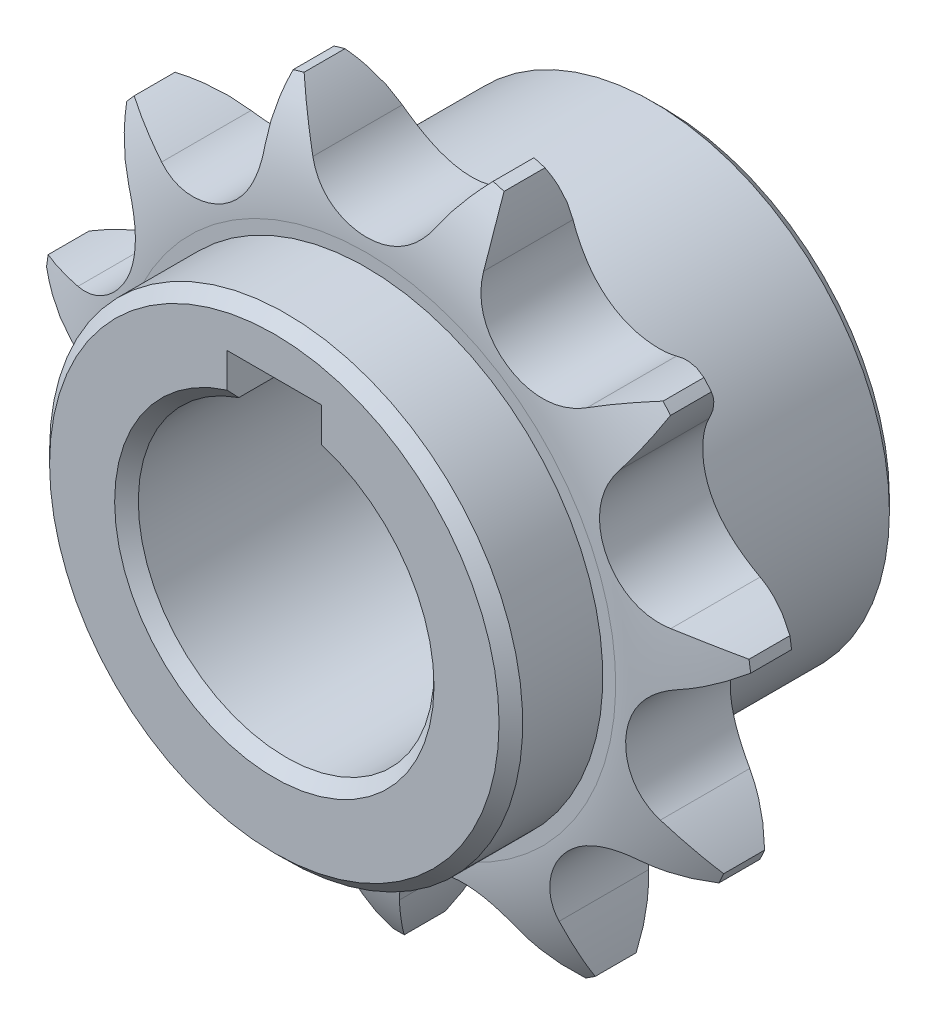
SolidWorks part; units mm, degrees
material "AISI 1045 钢，冷拔"
ref_plane "前视基准面" through (0, 0, 0) normal (0, 0, 1) x (1, 0, 0)
ref_plane "上视基准面" through (0, 0, 0) normal (0, 1, 0) x (1, 0, 0)
ref_plane "右视基准面" through (0, 0, 0) normal (1, 0, 0) x (0, 0, -1)
sketch "草图1" plane through (0, 0, 0) normal (0, 0, 1) x (1, 0, 0)
  line L0 (-28.1739, 0) -> (28.1739, 0) construction
  line L1 (0, 28.1739) -> (0, -28.1739) construction
  line L2 (0, 0) -> (15.232, 23.7014) construction
  line L3 (0, 28.1739) -> (24.3993, 14.087) construction
  line L4 (15.232, 23.7014) -> (-12.91, 25.042) construction
  line L5 (0, 22.1739) -> (0, 0)
  line L6 (0, 0) -> (11.9881, 18.6539)
  circle A0 centre (0, 0) radius 28.1739 construction
  arc A1 (0, 22.1739) -> (5.1962, 25.1739) centre (0, 28.1739) ccw
  arc A2 (9.2388, 23.9869) -> (11.9881, 18.6539) centre (15.232, 23.7014) ccw
  arc A3 (7.9868, 28.9173) -> (5.1962, 25.1739) centre (22.5167, 15.1739) ccw
  arc A4 (9.2388, 23.9869) -> (8.915, 28.6448) centre (-10.7386, 24.9385) ccw
  arc A5 (8.915, 28.6448) -> (7.9868, 28.9173) centre (0, 0) ccw
  dimension "D1" = 56.3478
  dimension "D3" = 12
  dimension "D4" = 12
  dimension "D7" = 40
  dimension "D8" = 40
  dimension "D9" = 60
  dimension "D2" = 32.727
  dimension "D5" = 60
  dimension "D6" = 60
extrude "凸台-拉伸1" add sketch "草图1" along normal blind 8.93
pattern_circular "阵列(圆周)1" count 11 over 360 about axis through (0, 0, 0) along (0, 0, 1) of "凸台-拉伸1"
sketch "草图2" plane through (0, 0, 0) normal (1, 0, 0) x (0, 0, -1)
  line L0 (-4.465, 28.9173) -> (-4.465, -29.9961) construction
  line L1 (-8.93, 28.9173) -> (0, 28.9173) construction
  line L2 (-8.93, -29.9961) -> (0, -29.9961) construction
  line L3 (-8.93, 28.9173) -> (-8.93, -29.9961) construction
  line L4 (0, 28.9173) -> (0, -29.9961) construction
  line L5 (-6.8663, 28.9173) -> (-6.8663, -29.9961) construction
  line L6 (0, 0) -> (-8.93, 0) construction
  line L10 (-2.0638, 28.9173) -> (-2.0638, -29.9961) construction
  line L11 (-8.93, 21.0901) -> (-8.93, 33.5648)
  line L12 (-8.93, 33.5648) -> (0, 33.5648)
  line L13 (0, 33.5648) -> (0, 21.0901)
  arc A1 (-4.465, 32.1277) -> (-8.93, 21.0901) centre (6.945, 21.0901) ccw
  arc A2 (0, 21.0901) -> (-4.465, 32.1277) centre (-15.875, 21.0901) ccw
  dimension "D3" = 31.75
  dimension "D4" = 31.75
  dimension "D1" = 2.0638
  dimension "D2" = 2.0638
revolve "切除-旋转1" cut sketch "草图2" angle 360 about L6
sketch "草图3" plane through (0, 0, 8.93) normal (0, 0, 1) x (1, 0, 0)
  circle A0 centre (0, 0) radius 20
  dimension "D1" = 40
extrude "凸台-拉伸2" add sketch "草图3" along normal blind 7.77
sketch "草图4" plane through (0, 0, 0) normal (0, 0, -1) x (-1, 0, 0)
  circle A0 centre (0, 0) radius 20
  dimension "D1" = 40
extrude "凸台-拉伸3" add sketch "草图4" along normal blind 16.3
sketch "草图5" plane through (0, 0, 16.7) normal (0, 0, 1) x (1, 0, 0)
  circle A0 centre (0, 0) radius 12.5
  dimension "D1" = 25
extrude "切除-拉伸1" cut sketch "草图5" against normal up to next
chamfer "倒角1" distance 1 angle 45 4 edges at (-12.5, 0, -16.3) (-20, 0, -16.3) (12.5, 0, 16.7) (20, 0, 16.7)
sketch "草图6" plane through (0, 0, 16.7) normal (0, 0, 1) x (1, 0, 0)
  line L0 (0, 0) -> (0, 30.3792) construction
  line L1 (4, 11.8427) -> (4, 15.8)
  line L2 (-4, 11.8427) -> (-4, 15.8)
  line L3 (-4, 15.8) -> (4, 15.8)
  line L5 (-4, 0) -> (-4, 30.3792) construction
  line L6 (4, 0) -> (4, 30.3792) construction
  circle A0 centre (0, 0) radius 12.5 construction
  arc A1 (4, 11.8427) -> (-4, 11.8427) centre (0, 0) ccw
  dimension "D1" = 4
  dimension "D3" = 15.8
  dimension "D2" = 4
extrude "切除-拉伸2" cut sketch "草图6" against normal up to next
sketch "草图7" plane through (0, 0, 0) normal (1, 0, 0) x (0, 0, -1)
  line L0 (35.3, 0) -> (-16.7, 0) construction
  line L1 (15.3, -20) -> (16.3, -19) construction
  line L2 (-16.7, 19) -> (-16.7, -19) construction
  line L3 (16.3, -19) -> (16.3, 19) construction
  circle A0 centre (8.3, 0) radius 3 construction
  point P11 (8.3, 0)
  dimension "D1" = 8
  dimension "D2" = 6
hole_wizard "M5 螺纹孔1" positions "3D草图1" profile "草图8" tap size "M5" standard "GB"
sketch3d "3D草图1"
  point P0 (-15.746, 12.3313, -7.1803)
sketch "草图8" plane through (-15.746, 12.3313, -7.1803) normal (0, 0, 1) x (-0.6166, -0.7873, 0)
  line L0 (0, 0) -> (0, 7.5)
  line L1 (0, 7.5) -> (2.1, 7.5)
  line L2 (2.1, 7.5) -> (2.1, 0)
  line L5 (2.1, 0) -> (0, 0)
  line L11 (0, -6.35) -> (0, 107.95) construction
  dimension "螺纹线主直径" = 4.2
  dimension "通孔螺纹孔钻头深度" = 7.5
